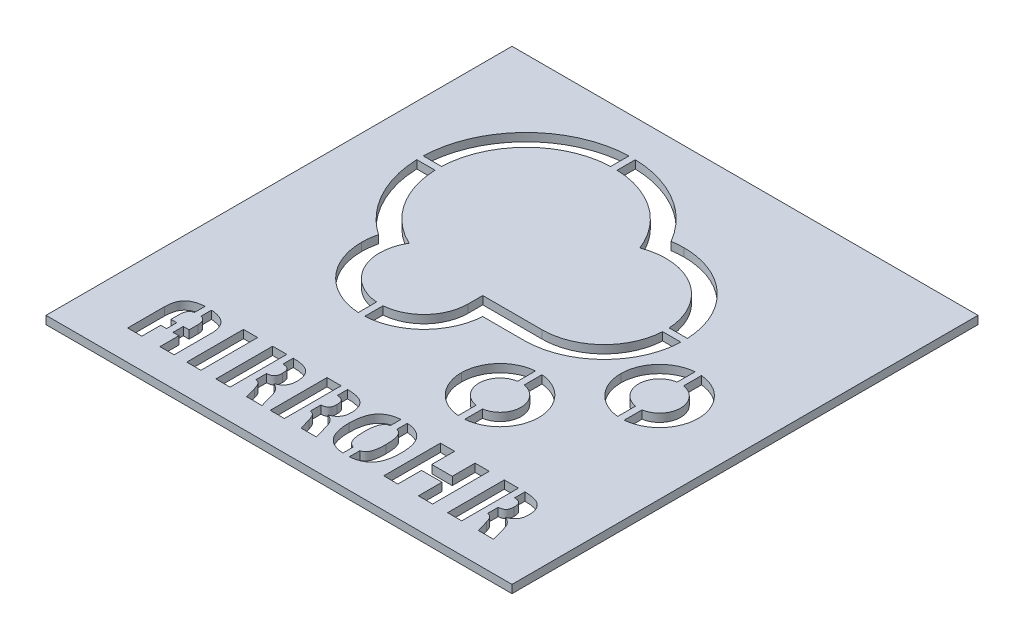
SolidWorks part; units mm, degrees
ref_plane "Front Plane" through (0, 0, 0) normal (0, 0, 1) x (1, 0, 0)
ref_plane "Top Plane" through (0, 0, 0) normal (0, 1, 0) x (1, 0, 0)
ref_plane "Right Plane" through (0, 0, 0) normal (1, 0, 0) x (0, 0, -1)
sketch "Logo" plane through (0, 0, 0) normal (0, 1, 0) x (1, 0, 0)
  line L0 (6.8222, -9.5648) -> (-7.8428, -9.5648)
  line L1 (-7.8428, -9.5648) -> (-7.8428, -13.1554)
  line L2 (-3.3693, -14.065) -> (6.822, -14.0654)
  line L4 (-45.0278, 38.3096) -> (45.0278, 38.3096) construction
  line L5 (-45.0278, 38.3096) -> (-45.0278, -38.3096) construction
  line L6 (-45.0278, -38.3096) -> (45.0278, -38.3096) construction
  line L7 (45.0278, 38.3096) -> (45.0278, -38.3096) construction
  spline S0 degree 3 poles (-18.8378, 33.8102) (-9.6328, 33.8102) (-1.7677, 28.0702) (1.3772, 19.9802) knots 0 0 0 0 1 1 1 1
  spline S1 degree 3 poles (1.3772, 19.9802) (3.0672, 20.6252) (4.9022, 20.9802) (6.8222, 20.9802) knots 1 1 1 1 2 2 2 2
  spline S2 degree 3 poles (6.8222, 20.9802) (15.2572, 20.9802) (22.0922, 14.1452) (22.0922, 5.7102) knots 2 2 2 2 3 3 3 3
  spline S3 degree 3 poles (22.0922, 5.7102) (22.0922, -2.7248) (15.2572, -9.5648) (6.8222, -9.5648) knots 3 3 3 3 4 4 4 4
  spline S4 degree 3 poles (-7.8428, -13.1554) (-7.8429, -19.1854) (-12.7331, -24.0753) (-18.7631, -24.0751) knots 6 6 6 6 7 7 7 7
  spline S5 degree 3 poles (-18.7631, -24.0751) (-24.7931, -24.0749) (-29.6829, -19.1848) (-29.6828, -13.1548) knots 7 7 7 7 8 8 8 8
  spline S6 degree 3 poles (-29.6828, -13.1548) (-29.6828, -11.0798) (-29.1028, -9.1398) (-28.0978, -7.4898) knots 8 8 8 8 9 9 9 9
  spline S7 degree 3 poles (-28.0978, -7.4898) (-35.4478, -4.0198) (-40.5278, 3.4602) (-40.5278, 12.1252) knots 9 9 9 9 10 10 10 10
  spline S8 degree 3 poles (-40.5278, 12.1252) (-40.5278, 24.1002) (-30.8178, 33.8102) (-18.8378, 33.8102) knots 10 10 10 10 11 11 11 11
  spline S9 degree 3 poles (-18.8378, 38.3096) (-33.279, 38.3096) (-45.0278, 26.5631) (-45.0278, 12.1246) knots 0 0 0 0 1 1 1 1
  spline S10 degree 3 poles (-45.0278, 12.1246) (-45.0278, 3.4834) (-40.7005, -4.5805) (-33.7243, -9.4193) knots 1 1 1 1 2 2 2 2
  spline S11 degree 3 poles (-33.7243, -9.4193) (-34.0275, -10.6346) (-34.1828, -11.8887) (-34.1828, -13.1554) knots 2 2 2 2 3 3 3 3
  spline S12 degree 3 poles (-34.1828, -13.1554) (-34.1828, -21.658) (-27.2654, -28.5754) (-18.7628, -28.5754) knots 3 3 3 3 4 4 4 4
  spline S13 degree 3 poles (-18.7628, -28.5754) (-10.5653, -28.5754) (-3.8414, -22.1461) (-3.3693, -14.065) knots 4 4 4 4 5 5 5 5
  spline S14 degree 3 poles (6.822, -14.0654) (17.7234, -14.0654) (26.5922, -5.1944) (26.5922, 5.7096) knots 6 6 6 6 7 7 7 7
  spline S15 degree 3 poles (26.5922, 5.7096) (26.5922, 16.6108) (17.7234, 25.4796) (6.8222, 25.4796) knots 7 7 7 7 8 8 8 8
  spline S16 degree 3 poles (6.8222, 25.4796) (5.8114, 25.4796) (4.8099, 25.4039) (3.8223, 25.2532) knots 8 8 8 8 9 9 9 9
  spline S17 degree 3 poles (3.8223, 25.2532) (1.9103, 28.5555) (-0.7065, 31.4051) (-3.8848, 33.6202) knots 9 9 9 9 10 10 10 10
  spline S18 degree 3 poles (-3.8848, 33.6202) (-8.2867, 36.688) (-13.4573, 38.3096) (-18.8378, 38.3096) knots 10 10 10 10 11 11 11 11
  spline S19 degree 3 poles (35.4472, -14.399) (32.584, -14.399) (30.2628, -12.0779) (30.2628, -9.2146) (30.2628, -6.3513) (32.584, -4.0302) (35.4472, -4.0302) knots 2 2 2 2 3 3 3 4 4 4 4
  spline S20 degree 3 poles (35.4472, -4.0302) (38.3105, -4.0302) (40.6316, -6.3513) (40.6316, -9.2146) (40.6316, -12.0779) (38.3105, -14.399) (35.4472, -14.399) knots 0 0 0 0 1 1 1 2 2 2 2
  spline S21 degree 3 poles (35.4472, 0.3545) (30.1708, 0.3545) (25.8782, -3.9382) (25.8782, -9.2146) knots 0 0 0 0 1 1 1 1
  spline S22 degree 3 poles (25.8782, -9.2146) (25.8782, -14.491) (30.1708, -18.7837) (35.4472, -18.7837) knots 1 1 1 1 2 2 2 2
  spline S23 degree 3 poles (35.4472, -18.7837) (40.7236, -18.7837) (45.0163, -14.491) (45.0163, -9.2146) knots 2 2 2 2 3 3 3 3
  spline S24 degree 3 poles (45.0163, -9.2146) (45.0163, -3.9382) (40.7236, 0.3545) (35.4472, 0.3545) knots 3 3 3 3 4 4 4 4
  spline S25 degree 3 poles (15.5836, -33.9035) (12.7203, -33.9035) (10.3992, -31.5824) (10.3992, -28.7191) (10.3992, -25.8559) (12.7203, -23.5347) (15.5836, -23.5347) knots 2 2 2 2 3 3 3 4 4 4 4
  spline S26 degree 3 poles (15.5836, -23.5347) (18.4468, -23.5347) (20.768, -25.8559) (20.768, -28.7191) (20.768, -31.5824) (18.4468, -33.9035) (15.5836, -33.9035) knots 0 0 0 0 1 1 1 2 2 2 2
  spline S27 degree 3 poles (15.5836, -19.1501) (10.3072, -19.1501) (6.0145, -23.4427) (6.0145, -28.7191) knots 0 0 0 0 1 1 1 1
  spline S28 degree 3 poles (6.0145, -28.7191) (6.0145, -33.9955) (10.3072, -38.2882) (15.5836, -38.2882) knots 1 1 1 1 2 2 2 2
  spline S29 degree 3 poles (15.5836, -38.2882) (20.86, -38.2882) (25.1526, -33.9955) (25.1526, -28.7191) knots 2 2 2 2 3 3 3 3
  spline S30 degree 3 poles (25.1526, -28.7191) (25.1526, -23.4427) (20.86, -19.1501) (15.5836, -19.1501) knots 3 3 3 3 4 4 4 4
  point P39 (0, 0)
  point P40 (45.0278, 0)
  point P41 (0, 38.3096)
sketch "Sketch4" plane through (0, 0, 0) normal (0, 1, 0) x (1, 0, 0)
  line L0 (-7.8428, -9.5648) -> (-7.8428, -13.1554) construction
  line L1 (-3.3693, -14.065) -> (6.822, -14.0654) construction
  line L2 (6.8222, -9.5648) -> (-7.8428, -9.5648) construction
  line L3 (-7.8428, -9.5648) -> (-7.8428, -13.1554)
  line L4 (-3.3693, -14.065) -> (6.822, -14.0654)
  line L5 (6.8222, -9.5648) -> (-7.8428, -9.5648)
  line L6 (-45.0278, 38.3096) -> (45.0278, 38.3096) construction
  line L7 (-57.5, 47.3096) -> (57.5, 47.3096)
  line L8 (-57.5, 47.3096) -> (-57.5, -67.6904)
  line L9 (-57.5, -67.6904) -> (57.5, -67.6904)
  line L10 (57.5, 47.3096) -> (57.5, -67.6904)
  line L11 (-57.5, -60.3243) -> (57.5, -60.3243) construction
  spline S0 degree 3 poles (-1563.1181, 2507.2411) (296.2295, -25.5053) (10.3992, -60.4928) (10.3992, -28.7191) (10.3992, 3.0546) (296.2339, -31.9301) (-1563.1617, -2564.7905) knots -8.096964 -8.096964 -8.096964 -8.096964 3 3 3 14.09705 14.09705 14.09705 14.09705 only from (15.5836, -33.9035) to (15.5836, -23.5347) construction
  spline S1 degree 3 poles (1594.2613, -2564.7108) (-265.0604, -31.9294) (20.768, 3.0543) (20.768, -28.7191) (20.768, -60.4931) (-265.0683, -25.5045) (1594.3389, 2507.3265) knots -10.096934 -10.096934 -10.096934 -10.096934 1 1 1 12.097089 12.097089 12.097089 12.097089 only from (15.5836, -23.5347) to (15.5836, -33.9035) construction
  spline S2 degree 3 poles (1460.132, 2576.6875) (-1926.2736, -2375.5534) (2362.3929, 1913.1024) (-2589.7209, -1473.1977) knots -6.113417 -6.113417 -6.113417 -6.113417 11.113298 11.113298 11.113298 11.113298 only from (15.5836, -38.2882) to (25.1526, -28.7191) construction
  spline S3 degree 3 poles (2620.9856, -1473.2612) (-2331.2474, 1913.1308) (1957.403, -2375.5206) (-1428.8942, 2576.577) knots -7.113406 -7.113406 -7.113406 -7.113406 10.113288 10.113288 10.113288 10.113288 only from (6.0145, -28.7191) to (15.5836, -38.2882) construction
  spline S4 degree 3 poles (-1428.9697, -2634.1257) (1957.4456, 2318.1152) (-2331.2307, -1970.5406) (2620.8928, 1415.7595) knots -8.113417 -8.113417 -8.113417 -8.113417 9.113298 9.113298 9.113298 9.113298 only from (15.5836, -19.1501) to (6.0145, -28.7191) construction
  spline S5 degree 3 poles (-2589.823, 1415.8293) (2362.4179, -1970.5763) (-1926.2379, 2318.0902) (1460.0622, -2634.0236) knots -5.113417 -5.113417 -5.113417 -5.113417 12.113298 12.113298 12.113298 12.113298 only from (25.1526, -28.7191) to (15.5836, -19.1501) construction
  spline S6 degree 3 poles (2640.8538, -1453.7631) (-2311.3871, 1932.6426) (1977.2687, -2356.024) (-1409.0314, 2596.0899) knots -7.113417 -7.113417 -7.113417 -7.113417 10.113298 10.113298 10.113298 10.113298 only from (25.8782, -9.2146) to (35.4472, -18.7837) construction
  spline S7 degree 3 poles (-1543.2917, 2526.7312) (316.0935, -6.0009) (30.2628, -40.9882) (30.2628, -9.2146) (30.2628, 22.5593) (316.0981, -12.4284) (-1543.337, -2545.2311) knots -8.096943 -8.096943 -8.096943 -8.096943 3 3 3 14.097033 14.097033 14.097033 14.097033 only from (35.4472, -14.399) to (35.4472, -4.0302) construction
  spline S8 degree 3 poles (1614.1399, -2545.1838) (-245.1982, -12.428) (40.6316, 22.5591) (40.6316, -9.2146) (40.6316, -40.9885) (-245.2027, -6.0002) (1614.1834, 2526.805) knots -10.096964 -10.096964 -10.096964 -10.096964 1 1 1 12.09705 12.09705 12.09705 12.09705 only from (35.4472, -4.0302) to (35.4472, -14.399) construction
  spline S9 degree 3 poles (1479.9957, 2596.192) (-1906.41, -2356.0489) (2382.2566, 1932.6069) (-2569.8572, -1453.6932) knots -6.113417 -6.113417 -6.113417 -6.113417 11.113298 11.113298 11.113298 11.113298 only from (35.4472, -18.7837) to (45.0163, -9.2146) construction
  spline S10 degree 3 poles (-2569.9594, 1435.3387) (2382.2815, -1951.0767) (-1906.3743, 2337.5997) (1479.9259, -2614.5239) knots -5.113417 -5.113417 -5.113417 -5.113417 12.113298 12.113298 12.113298 12.113298 only from (45.0163, -9.2146) to (35.4472, 0.3545) construction
  spline S11 degree 3 poles (-1409.0948, -2614.6166) (1977.2971, 2337.6164) (-2311.3542, -1951.034) (2640.7433, 1435.2632) knots -8.113406 -8.113406 -8.113406 -8.113406 9.113288 9.113288 9.113288 9.113288 only from (35.4472, 0.3545) to (25.8782, -9.2146) construction
  spline S12 degree 3 poles (2687.9195, 1203.4807) (-2446.2841, -1870.2517) (1861.9201, 2440.7726) (-1208.2564, -2695.4033) knots 3.937482 3.937482 3.937482 3.937482 17.062235 17.062235 17.062235 17.062235 only from (-40.5278, 12.1252) to (-18.8378, 33.8102) construction
  spline S13 degree 3 poles (-1146.2521, -2713.887) (1850.0041, 2462.8367) (-2469.9297, -1856.203) (2707.2807, 1139.0758) knots -5.645374 -5.645374 -5.645374 -5.645374 6.645042 6.645042 6.645042 6.645042 only from (-18.8378, 38.3096) to (-45.0278, 12.1246) construction
  spline S14 degree 3 poles (2391.1864, -1692.7249) (-2002.7517, 2377.3435) (1274.203, -2791.9559) (-532.9439, 2921.2731) knots -8.245789 -8.245789 -8.245789 -8.245789 11.415145 11.415145 11.415145 11.415145 only from (-45.0278, 12.1246) to (-33.7243, -9.4193) construction
  spline S15 degree 3 poles (-1203.0444, 2726.4883) (1857.5978, -2422.8591) (-2442.9291, 1900.2261) (2685.5379, -1184.1756) knots 0.236451 0.236451 0.236451 0.236451 18.38266 18.38266 18.38266 18.38266 only from (-28.0978, -7.4898) to (-40.5278, 12.1252) construction
  spline S16 degree 3 poles (2602.1303, 1397.6362) (-2378.1491, -1949.1531) (1918.6495, 2348.8318) (-1435.6923, -2640.3784) knots -14.455557 -14.455557 -14.455557 -14.455557 33.350301 33.350301 33.350301 33.350301 only from (-29.6828, -13.1548) to (-28.0978, -7.4898) construction
  spline S17 degree 3 poles (214.4881, -2977.5634) (449.8224, 3000.5485) (-1185.1093, -2829.6682) (1722.3591, 2392.541) knots -45.752091 -45.752091 -45.752091 -45.752091 49.547523 49.547523 49.547523 49.547523 only from (-33.7243, -9.4193) to (-34.1828, -13.1554) construction
  spline S18 degree 3 poles (2644.7906, -1323.6407) (-2409.7939, 1897.8056) (1892.1649, -2404.1834) (-1329.1976, 2650.3473) knots -3.84167 -3.84167 -3.84167 -3.84167 10.84161 10.84161 10.84161 10.84161 only from (-34.1828, -13.1554) to (-18.7628, -28.5754) construction
  spline S19 degree 3 poles (-1423.9537, 2610.6341) (1912.8518, -2371.6713) (-2377.1155, 1918.631) (2604.8722, -1418.524) knots -0.758808 -0.758808 -0.758808 -0.758808 15.758776 15.758776 15.758776 15.758776 only from (-18.7631, -24.0751) to (-29.6828, -13.1548) construction
  spline S20 degree 3 poles (-2642.5299, -1418.3835) (2339.7195, 1918.4855) (-1950.5068, -2371.5174) (1386.5613, 2610.4702) knots -1.758788 -1.758788 -1.758788 -1.758788 14.758714 14.758714 14.758714 14.758714 only from (-7.8428, -13.1554) to (-18.7631, -24.0751) construction
  spline S21 degree 3 poles (1291.8934, 2650.2912) (-1929.9587, -2404.068) (2372.5701, 1897.6329) (-2682.6404, -1323.4175) knots -3.096668 -3.096668 -3.096668 -3.096668 12.133918 12.133918 12.133918 12.133918 only from (-18.7628, -28.5754) to (-3.3693, -14.065) construction
  spline S22 degree 3 poles (1235.9369, 2699.4183) (-1885.1295, -2412.1699) (2424.1402, 1898.3378) (-2686.577, -1224.0265) knots -0.253933 -0.253933 -0.253933 -0.253933 13.254292 13.254292 13.254292 13.254292 only from (6.822, -14.0654) to (26.5922, 5.7096) construction
  spline S23 degree 3 poles (-2657.0297, -1304.1441) (2395.1026, 1916.7716) (-1899.6373, -2386.2468) (1311.6988, 2671.9485) knots -3.883603 -3.883603 -3.883603 -3.883603 10.882064 10.882064 10.882064 10.882064 only from (22.0922, 5.7102) to (6.8222, -9.5648) construction
  spline S24 degree 3 poles (1313.6625, -2659.6639) (-1901.6986, 2395.875) (2396.9632, -1902.8095) (-2658.4961, 1312.5371) knots -4.885072 -4.885072 -4.885072 -4.885072 9.885031 9.885031 9.885031 9.885031 only from (6.8222, 20.9802) to (22.0922, 5.7102) construction
  spline S25 degree 3 poles (2616.089, 1453.3855) (-2310.1363, -2015.9175) (1831.1355, 2474.405) (-1214.6176, -2700.559) knots -32.679312 -32.679312 -32.679312 -32.679312 32.027034 32.027034 32.027034 32.027034 only from (1.3772, 19.9802) to (6.8222, 20.9802) construction
  spline S26 degree 3 poles (-2120.1619, -2019.1293) (2659.5519, 1065.2455) (-2852.9999, 43.9931) (2729.2966, -1106.8439) knots -75.028946 -75.028946 -75.028946 -75.028946 93.179941 93.179941 93.179941 93.179941 only from (6.8222, 25.4796) to (3.8223, 25.2532) construction
  spline S27 degree 3 poles (-2686.7092, 1235.1871) (2424.4098, -1886.5908) (-1885.492, 2423.2889) (1236.3167, -2687.8204) knots 0.745633 0.745633 0.745633 0.745633 14.254374 14.254374 14.254374 14.254374 only from (26.5922, 5.7096) to (6.8222, 25.4796) construction
  spline S28 degree 3 poles (-2686.4652, 1266.0216) (2203.0185, -2039.9601) (-1492.4842, 2651.6057) (567.9184, -2873.2867) knots -13.877405 -13.877405 -13.877405 -13.877405 32.557755 32.557755 32.557755 32.557755 only from (3.8223, 25.2532) to (-3.8848, 33.6202) construction
  spline S29 degree 3 poles (-2914.0606, -511.8571) (2955.6046, -405.3584) (-2699.1603, 1366.4164) (2055.3883, -2073.9653) knots -6.478561 -6.478561 -6.478561 -6.478561 27.50147 27.50147 27.50147 27.50147 only from (-3.8848, 33.6202) to (-18.8378, 38.3096) construction
  spline S30 degree 3 poles (1169.0079, -2696.1689) (-1898.0758, 2443.8133) (2408.0009, -1875.2213) (-2726.461, 1209.6782) knots -7.88221 -7.88221 -7.88221 -7.88221 9.188291 9.188291 9.188291 9.188291 only from (-18.8378, 33.8102) to (1.3772, 19.9802) construction
  spline S31 degree 3 poles (15.5836, -33.9035) (12.7203, -33.9035) (10.3992, -31.5824) (10.3992, -28.7191) (10.3992, -25.8559) (12.7203, -23.5347) (15.5836, -23.5347) knots 2 2 2 2 3 3 3 4 4 4 4
  spline S32 degree 3 poles (15.5836, -23.5347) (18.4468, -23.5347) (20.768, -25.8559) (20.768, -28.7191) (20.768, -31.5824) (18.4468, -33.9035) (15.5836, -33.9035) knots 0 0 0 0 1 1 1 2 2 2 2
  spline S33 degree 3 poles (15.5836, -38.2882) (20.86, -38.2882) (25.1526, -33.9955) (25.1526, -28.7191) knots 2 2 2 2 3 3 3 3
  spline S34 degree 3 poles (6.0145, -28.7191) (6.0145, -33.9955) (10.3072, -38.2882) (15.5836, -38.2882) knots 1 1 1 1 2 2 2 2
  spline S35 degree 3 poles (15.5836, -19.1501) (10.3072, -19.1501) (6.0145, -23.4427) (6.0145, -28.7191) knots 0 0 0 0 1 1 1 1
  spline S36 degree 3 poles (25.1526, -28.7191) (25.1526, -23.4427) (20.86, -19.1501) (15.5836, -19.1501) knots 3 3 3 3 4 4 4 4
  spline S37 degree 3 poles (25.8782, -9.2146) (25.8782, -14.491) (30.1708, -18.7837) (35.4472, -18.7837) knots 1 1 1 1 2 2 2 2
  spline S38 degree 3 poles (35.4472, -14.399) (32.584, -14.399) (30.2628, -12.0779) (30.2628, -9.2146) (30.2628, -6.3513) (32.584, -4.0302) (35.4472, -4.0302) knots 2 2 2 2 3 3 3 4 4 4 4
  spline S39 degree 3 poles (35.4472, -4.0302) (38.3105, -4.0302) (40.6316, -6.3513) (40.6316, -9.2146) (40.6316, -12.0779) (38.3105, -14.399) (35.4472, -14.399) knots 0 0 0 0 1 1 1 2 2 2 2
  spline S40 degree 3 poles (35.4472, -18.7837) (40.7236, -18.7837) (45.0163, -14.491) (45.0163, -9.2146) knots 2 2 2 2 3 3 3 3
  spline S41 degree 3 poles (45.0163, -9.2146) (45.0163, -3.9382) (40.7236, 0.3545) (35.4472, 0.3545) knots 3 3 3 3 4 4 4 4
  spline S42 degree 3 poles (35.4472, 0.3545) (30.1708, 0.3545) (25.8782, -3.9382) (25.8782, -9.2146) knots 0 0 0 0 1 1 1 1
  spline S43 degree 3 poles (-40.5278, 12.1252) (-40.5278, 24.1002) (-30.8178, 33.8102) (-18.8378, 33.8102) knots 10 10 10 10 11 11 11 11
  spline S44 degree 3 poles (-18.8378, 38.3096) (-33.279, 38.3096) (-45.0278, 26.5631) (-45.0278, 12.1246) knots 0 0 0 0 1 1 1 1
  spline S45 degree 3 poles (-45.0278, 12.1246) (-45.0278, 3.4834) (-40.7005, -4.5805) (-33.7243, -9.4193) knots 1 1 1 1 2 2 2 2
  spline S46 degree 3 poles (-28.0978, -7.4898) (-35.4478, -4.0198) (-40.5278, 3.4602) (-40.5278, 12.1252) knots 9 9 9 9 10 10 10 10
  spline S47 degree 3 poles (-29.6828, -13.1548) (-29.6828, -11.0798) (-29.1028, -9.1398) (-28.0978, -7.4898) knots 8 8 8 8 9 9 9 9
  spline S48 degree 3 poles (-33.7243, -9.4193) (-34.0275, -10.6346) (-34.1828, -11.8887) (-34.1828, -13.1554) knots 2 2 2 2 3 3 3 3
  spline S49 degree 3 poles (-34.1828, -13.1554) (-34.1828, -21.658) (-27.2654, -28.5754) (-18.7628, -28.5754) knots 3 3 3 3 4 4 4 4
  spline S50 degree 3 poles (-18.7631, -24.0751) (-24.7931, -24.0749) (-29.6829, -19.1848) (-29.6828, -13.1548) knots 7 7 7 7 8 8 8 8
  spline S51 degree 3 poles (-7.8428, -13.1554) (-7.8429, -19.1854) (-12.7331, -24.0753) (-18.7631, -24.0751) knots 6 6 6 6 7 7 7 7
  spline S52 degree 3 poles (-18.7628, -28.5754) (-10.5653, -28.5754) (-3.8414, -22.1461) (-3.3693, -14.065) knots 4 4 4 4 5 5 5 5
  spline S53 degree 3 poles (6.822, -14.0654) (17.7234, -14.0654) (26.5922, -5.1944) (26.5922, 5.7096) knots 6 6 6 6 7 7 7 7
  spline S54 degree 3 poles (22.0922, 5.7102) (22.0922, -2.7248) (15.2572, -9.5648) (6.8222, -9.5648) knots 3 3 3 3 4 4 4 4
  spline S55 degree 3 poles (6.8222, 20.9802) (15.2572, 20.9802) (22.0922, 14.1452) (22.0922, 5.7102) knots 2 2 2 2 3 3 3 3
  spline S56 degree 3 poles (1.3772, 19.9802) (3.0672, 20.6252) (4.9022, 20.9802) (6.8222, 20.9802) knots 1 1 1 1 2 2 2 2
  spline S57 degree 3 poles (6.8222, 25.4796) (5.8114, 25.4796) (4.8099, 25.4039) (3.8223, 25.2532) knots 8 8 8 8 9 9 9 9
  spline S58 degree 3 poles (26.5922, 5.7096) (26.5922, 16.6108) (17.7234, 25.4796) (6.8222, 25.4796) knots 7 7 7 7 8 8 8 8
  spline S59 degree 3 poles (3.8223, 25.2532) (1.9103, 28.5555) (-0.7065, 31.4051) (-3.8848, 33.6202) knots 9 9 9 9 10 10 10 10
  spline S60 degree 3 poles (-3.8848, 33.6202) (-8.2867, 36.688) (-13.4573, 38.3096) (-18.8378, 38.3096) knots 10 10 10 10 11 11 11 11
  spline S61 degree 3 poles (-18.8378, 33.8102) (-9.6328, 33.8102) (-1.7677, 28.0702) (1.3772, 19.9802) knots 0 0 0 0 1 1 1 1
  text T0 "LUFTDATA.SE" font "3ds" height 11
  point P10 (0, 47.3096)
  dimension "D1" = 115
  dimension "D2" = 115
  dimension "D3" = 9
extrude "Boss-Extrude2" add sketch "Sketch4" along normal blind 2 contours L8 L11 L10 L7 S60 S59 S57 S58 S53 L4 S52 S49 S48 S45 S44 S42 S41 S40 S37 S36 S33 S34 S35 | L11 L8 L9 L10 | S61 S43 S46 S47 S50 S51 L3 L5 S54 S55 S56 | S32 S31 | S39 S38
sketch "Sketch5" plane through (0, 2, 0) normal (0, 1, 0) x (1, 0, 0)
  text T0 "<b>AIRROHR</b>" font "3ds" height 14
extrude "Cut-Extrude1" cut sketch "Sketch5" against normal up to next (2 mm away)
sketch "Sketch6" plane through (0, 2, 0) normal (0, 1, 0) x (1, 0, 0)
  line L1 (-19.6378, 31.1469) -> (-18.0378, 31.1469)
  line L2 (-19.6378, 31.1469) -> (-19.6378, 40.1633)
  line L3 (-19.6378, 40.1633) -> (-18.0378, 40.1633)
  line L4 (-18.0378, 31.1469) -> (-18.0378, 40.1633)
  line L5 (-19.6378, 31.1469) -> (-18.0378, 40.1633) construction
  line L6 (-19.6378, 40.1633) -> (-18.0378, 31.1469) construction
  line L7 (-48.9036, 12.9246) -> (-36.3551, 12.9246)
  line L8 (-48.9036, 12.9246) -> (-48.9036, 11.3246)
  line L9 (-48.9036, 11.3246) -> (-36.3551, 11.3246)
  line L10 (-36.3551, 12.9246) -> (-36.3551, 11.3246)
  line L11 (-48.9036, 12.9246) -> (-36.3551, 11.3246) construction
  line L12 (-48.9036, 11.3246) -> (-36.3551, 12.9246) construction
  line L13 (20.6999, 6.5102) -> (28.6008, 6.5102)
  line L14 (20.6999, 6.5102) -> (20.6999, 4.9102)
  line L15 (20.6999, 4.9102) -> (28.6008, 4.9102)
  line L16 (28.6008, 6.5102) -> (28.6008, 4.9102)
  line L17 (20.6999, 6.5102) -> (28.6008, 4.9102) construction
  line L18 (20.6999, 4.9102) -> (28.6008, 6.5102) construction
  line L19 (-19.5631, -31.8281) -> (-17.9631, -31.8281)
  line L20 (-19.5631, -31.8281) -> (-19.5631, -20.9935)
  line L21 (-19.5631, -20.9935) -> (-17.9631, -20.9935)
  line L22 (-17.9631, -31.8281) -> (-17.9631, -20.9935)
  line L23 (-19.5631, -31.8281) -> (-17.9631, -20.9935) construction
  line L24 (-19.5631, -20.9935) -> (-17.9631, -31.8281) construction
  line L25 (34.6472, -21.0813) -> (36.2472, -21.0813)
  line L26 (34.6472, -21.0813) -> (34.6472, 2.6569)
  line L27 (34.6472, 2.6569) -> (36.2472, 2.6569)
  line L28 (36.2472, -21.0813) -> (36.2472, 2.6569)
  line L29 (34.6472, -21.0813) -> (36.2472, 2.6569) construction
  line L30 (34.6472, 2.6569) -> (36.2472, -21.0813) construction
  line L31 (14.7836, -40.0383) -> (16.3836, -40.0383)
  line L32 (14.7836, -40.0383) -> (14.7836, -16.2942)
  line L33 (14.7836, -16.2942) -> (16.3836, -16.2942)
  line L34 (16.3836, -40.0383) -> (16.3836, -16.2942)
  line L35 (14.7836, -40.0383) -> (16.3836, -16.2942) construction
  line L36 (14.7836, -16.2942) -> (16.3836, -40.0383) construction
  point P0 (-18.8378, 35.6551)
  point P5 (24.6504, 5.7102)
  point P7 (-42.6293, 12.1246)
  point P16 (-18.7631, -26.4108)
  point P21 (35.4472, -9.2122)
  point P26 (15.5836, -28.1663)
  dimension "D1" = 1.6
extrude "Boss-Extrude3" add sketch "Sketch6" against normal through all
sketch "Sketch7" plane through (0, 2, 0) normal (0, 1, 0) x (1, 0, 0)
  line L0 (-41.2222, -53.1298) -> (-36.75, -53.1298) construction
  line L2 (-39.7861, -43.1298) -> (-39.7861, -63.3243)
  line L3 (-39.7861, -63.3243) -> (-38.1861, -63.3243)
  line L4 (-38.1861, -43.1298) -> (-38.1861, -63.3243)
  line L5 (-19.4444, -43.1298) -> (-17.8444, -43.1298)
  line L6 (-19.4444, -43.1298) -> (-19.4444, -63.3243)
  line L7 (-19.4444, -63.3243) -> (-17.8444, -63.3243)
  line L8 (-17.8444, -43.1298) -> (-17.8444, -63.3243)
  line L9 (-6.0278, -43.1298) -> (-4.4278, -43.1298)
  line L10 (-6.0278, -43.1298) -> (-6.0278, -63.3243)
  line L11 (-6.0278, -63.3243) -> (-4.4278, -63.3243)
  line L12 (-4.4278, -43.1298) -> (-4.4278, -63.3243)
  line L13 (8.5546, -43.1298) -> (10.1546, -43.1298)
  line L14 (8.5546, -43.1298) -> (8.5546, -63.3243)
  line L15 (8.5546, -63.3243) -> (10.1546, -63.3243)
  line L16 (10.1546, -43.1298) -> (10.1546, -63.3243)
  line L17 (37.7222, -43.1298) -> (39.3222, -43.1298)
  line L18 (37.7222, -43.1298) -> (37.7222, -63.3243)
  line L19 (37.7222, -63.3243) -> (39.3222, -63.3243)
  line L20 (39.3222, -43.1298) -> (39.3222, -63.3243)
  line L21 (-39.7861, -43.1298) -> (-38.1861, -43.1298)
  line L22 (-41.2222, -60.3243) -> (-44.7222, -60.3243) construction
  line L23 (-36.75, -55.6576) -> (-41.2222, -55.6576) construction
  line L24 (-19.4444, -48.852) -> (-19.4444, -52.8746) construction
  line L25 (-6.0278, -48.852) -> (-6.0278, -52.8746) construction
  line L26 (37.7222, -48.852) -> (37.7222, -52.8746) construction
  point P25 (-38.9861, -53.1298)
  point P26 (-38.9861, -55.6576)
  point P29 (-38.9861, -43.1298)
  point P35 (9.3546, -43.1298)
  dimension "D1" = 3
  dimension "D2" = 3
  dimension "D3" = 1.6
extrude "Boss-Extrude4" add sketch "Sketch7" against normal up to surface (2 mm away) up to face at (18.1374, 0, 29.6017)
